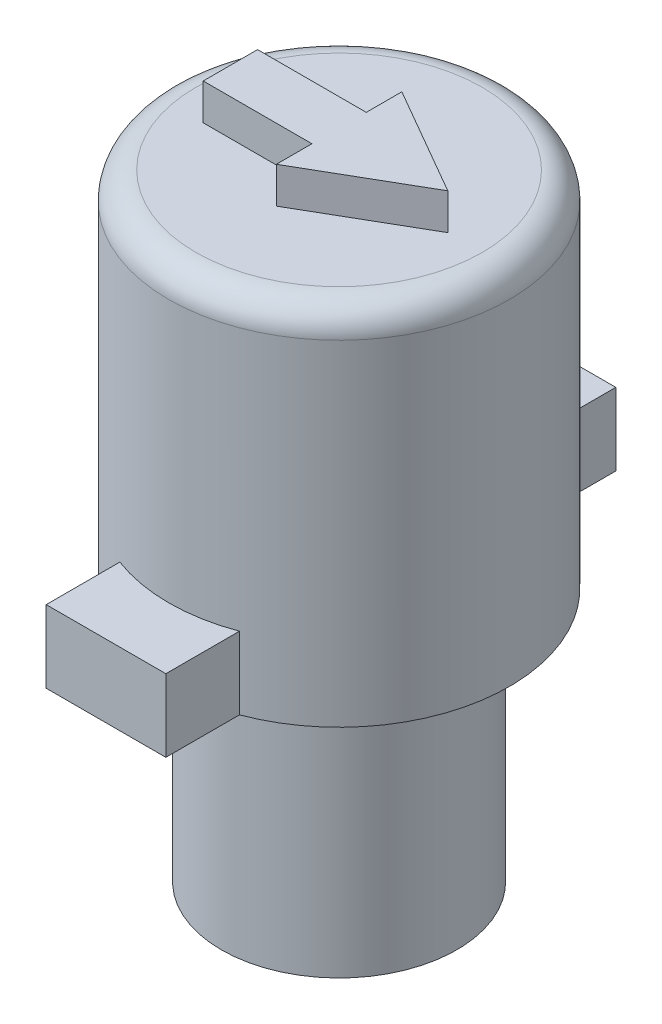
SolidWorks part; units mm, degrees
ref_plane "Front Plane" through (0, 0, 0) normal (0, 0, 1) x (1, 0, 0)
ref_plane "Top Plane" through (0, 0, 0) normal (0, 1, 0) x (1, 0, 0)
ref_plane "Right Plane" through (0, 0, 0) normal (1, 0, 0) x (0, 0, -1)
sketch "Sketch1" plane through (0, 0, 0) normal (0, 1, 0) x (1, 0, 0)
  circle A0 centre (0, 0) radius 3.25
  dimension "D1" = 6.5
extrude "Boss-Extrude1" add sketch "Sketch1" along normal blind 7.018 contours A0
sketch "Sketch2" plane through (0, 0, 0) normal (0, -1, 0) x (1, 0, 0)
  circle A1 centre (0, 0) radius 1.75
  dimension "D1" = 3.5
extrude "Cut-Extrude1" [suppressed] cut sketch "Sketch2" against normal blind 2.5
sketch "Sketch6" plane through (0, 7.018, 0) normal (0, 1, 0) x (1, 0, 0)
  circle A0 centre (0, 0) radius 4.7
  dimension "D1" = 9.4
extrude "Boss-Extrude2" add sketch "Sketch6" along normal blind 10 contours A0
fillet "Fillet1" radius 0.75 1 edges at (0, 17.018, 4.7)
sketch "Sketch7" plane through (0, 17.018, 0) normal (0, 1, 0) x (1, 0, 0)
  line L0 (0, 0) -> (-3, 0) construction
  line L1 (0, 0) -> (1, 0) construction
  line L2 (0, 0) -> (1, 0) construction
  line L3 (3, 0) -> (0, 1.7321)
  line L4 (0, 1.7321) -> (0, -1.7321)
  line L5 (0, -1.7321) -> (3, 0)
  line L6 (1, 0) -> (3, 0) construction
  line L7 (-3, 0) -> (-3, 0.75)
  line L8 (-3, 0.75) -> (0, 0.75)
  line L9 (0, 0.75) -> (0, -0.75)
  line L10 (0, -0.75) -> (-3, -0.75)
  line L11 (-3, -0.75) -> (-3, 0)
  circle A0 centre (1, 0) radius 1 construction
  dimension "D1" = 1
  dimension "D2" = 2
  dimension "D3" = 3
  dimension "D4" = 0.75
  dimension "D5" = 0.75
sketch "Sketch8" plane through (0, 17.018, 0) normal (0, 1, 0) x (1, 0, 0)
  line L0 (0, 0.75) -> (-3, 0.75)
  line L1 (-3, 0.75) -> (-3, -0.75)
  line L2 (-3, -0.75) -> (0, -0.75)
  line L3 (0, -0.75) -> (0, -1.7321)
  line L4 (0, -1.7321) -> (3, 0)
  line L5 (3, 0) -> (0, 1.7321)
  line L6 (0, 1.7321) -> (0, 0.75)
extrude "Boss-Extrude3" add sketch "Sketch8" along normal blind 1
sketch "Sketch9" plane through (0, 7.018, 0) normal (0, -1, 0) x (1, 0, 0)
  line L0 (0, 4.7) -> (0, -4.7) construction
  line L7 (-1.651, 4.4005) -> (-1.651, 6.4325)
  line L8 (-1.651, 6.4325) -> (1.651, 6.4325)
  line L9 (1.651, 6.4325) -> (1.651, 4.4005)
  line L10 (-1.016, -4.5889) -> (-1.016, -6.6209)
  line L11 (-1.016, -6.6209) -> (1.016, -6.6209)
  line L12 (1.016, -6.6209) -> (1.016, -4.5889)
  circle A1 centre (0, 0) radius 4.7 construction
  arc A3 (-1.016, -4.5889) -> (1.016, -4.5889) centre (0, 0) ccw
  arc A4 (1.651, 4.4005) -> (-1.651, 4.4005) centre (0, 0) ccw
  dimension "D2" = 2.032
  dimension "D3" = 2.032
  dimension "D4" = 2.032
  dimension "D1" = 3.302
extrude "Boss-Extrude4" add sketch "Sketch9" against normal blind 2
